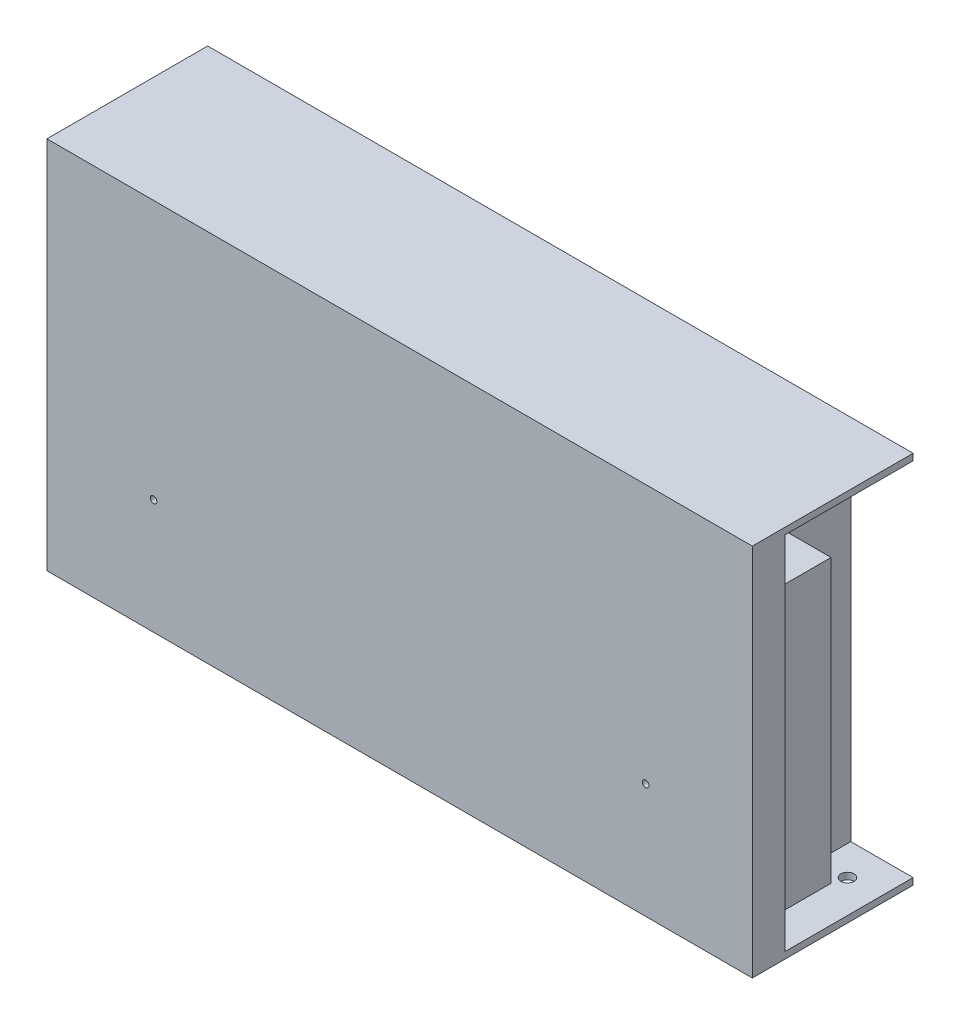
SolidWorks part; units mm, degrees
ref_plane "Ön Düzlem" through (0, 0, 0) normal (0, 0, 1) x (1, 0, 0)
ref_plane "Üst Düzlem" through (0, 0, 0) normal (0, 1, 0) x (1, 0, 0)
ref_plane "Sağ Düzlem" through (0, 0, 0) normal (1, 0, 0) x (0, 0, -1)
sketch "Sketch1" plane through (0, 0, 0) normal (0, 0, 1) x (1, 0, 0)
  line L1 (-107.5, -57) -> (107.5, -57)
  line L2 (-107.5, -57) -> (-107.5, 57)
  line L3 (-107.5, 57) -> (107.5, 57)
  line L4 (107.5, -57) -> (107.5, 57)
  line L5 (-107.5, -57) -> (107.5, 57) construction
  line L6 (-107.5, 57) -> (107.5, -57) construction
  point P0 (0, 0)
  dimension "D1" = 114
  dimension "D2" = 215
extrude "Boss-Extrude1" add sketch "Sketch1" along normal blind 49
sketch "Sketch2" plane through (0, 0, 0) normal (0, 0, -1) x (-1, 0, 0)
  line L0 (-107.5, 55) -> (-88.5, 55)
  line L1 (-107.5, -57) -> (-107.5, 57) construction
  line L2 (-88.5, 55) -> (-88.5, -55)
  line L3 (-88.5, -55) -> (-107.5, -55)
  line L4 (-107.5, -55) -> (-107.5, 55)
  line L5 (-107.5, 57) -> (107.5, 57) construction
  line L6 (107.5, -57) -> (-107.5, -57) construction
  dimension "D1" = 2
  dimension "D2" = 2
  dimension "D3" = 19
extrude "Cut-Extrude1" cut sketch "Sketch2" against normal blind 39
sketch "Sketch3" plane through (0, 0, 39) normal (0, 0, -1) x (-1, 0, 0)
  line L0 (-88.5, -48) -> (-103.5, -48)
  line L1 (-88.5, -55) -> (-88.5, 55) construction
  line L2 (-103.5, -48) -> (-103.5, 38)
  line L3 (-103.5, 38) -> (-88.5, 38)
  line L4 (-88.5, 38) -> (-88.5, -48)
  line L5 (-88.5, 55) -> (-107.5, 55) construction
  line L6 (-107.5, -55) -> (-88.5, -55) construction
  dimension "D1" = 17
  dimension "D2" = 7
  dimension "D3" = 15
extrude "Boss-Extrude3" add sketch "Sketch3" along normal blind 18
sketch "Sketch4" plane through (0, -55, 0) normal (0, 1, 0) x (1, 0, 0)
  line L0 (107.5, -49) -> (107.5, 0) construction
  line L1 (107.5, 0) -> (-107.5, 0) construction
  circle A0 centre (97.5, -10) radius 2
  point P6 (99.5, -9.5694)
  dimension "D1" = 4
  dimension "D2" = 10
  dimension "D3" = 10
extrude "Cut-Extrude2" cut sketch "Sketch4" against normal blind 8
sketch "Sketch5" plane through (0, 0, 49) normal (0, 0, 1) x (1, 0, 0)
  line L0 (107.5, -57) -> (107.5, 57) construction
  line L2 (-107.5, -57) -> (107.5, -57) construction
  circle A0 centre (75, -22) radius 1
  circle A1 centre (-75, -22) radius 1
  point P4 (0, 0)
  dimension "D1" = 2
  dimension "D2" = 150
  dimension "D3" = 32.5
  dimension "D4" = 35
extrude "Cut-Extrude3" cut sketch "Sketch5" against normal blind 2
